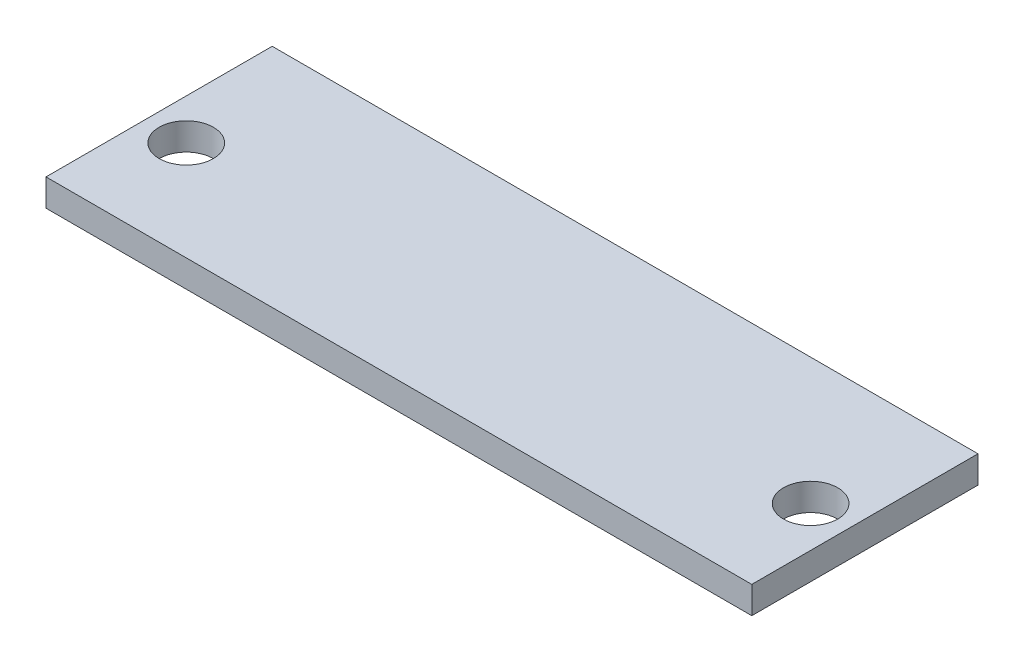
SolidWorks part; units mm, degrees
ref_plane "Front Plane" through (0, 0, 0) normal (0, 0, 1) x (1, 0, 0)
ref_plane "Top Plane" through (0, 0, 0) normal (0, 1, 0) x (1, 0, 0)
ref_plane "Right Plane" through (0, 0, 0) normal (1, 0, 0) x (0, 0, -1)
sketch "Sketch1" plane through (0, 0, 0) normal (0, 1, 0) x (1, 0, 0)
  line L1 (-40.9679, 23.8672) -> (37.0321, 23.8672)
  line L2 (-40.9679, 23.8672) -> (-40.9679, -1.1328)
  line L3 (-40.9679, -1.1328) -> (37.0321, -1.1328)
  line L4 (37.0321, 23.8672) -> (37.0321, -1.1328)
  circle A0 centre (-36.4679, 9.8672) radius 3
  circle A1 centre (32.5321, 9.8672) radius 3
  dimension "D3" = 14
  dimension "D4" = 4.5
  dimension "D5" = 4.5
  dimension "D1" = 78
  dimension "D2" = 25
  dimension "D6" = 14
extrude "Boss-Extrude1" add sketch "Sketch1" along normal blind 3
